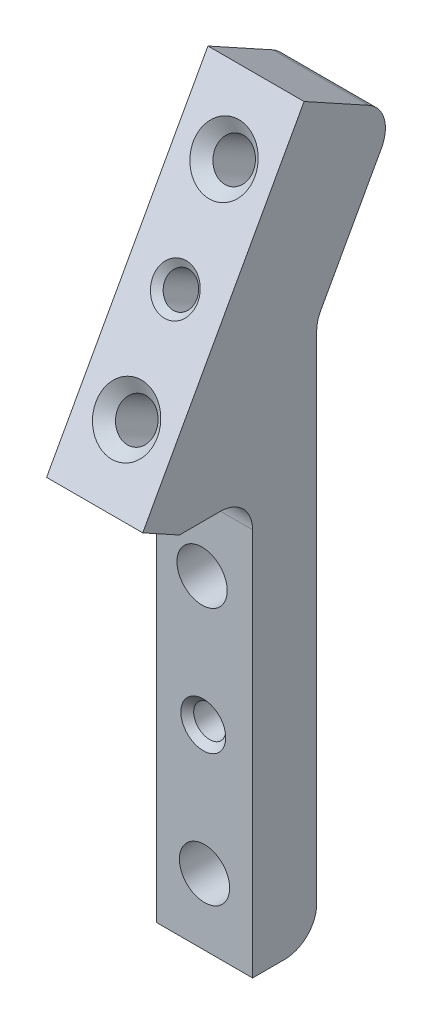
SolidWorks part; units mm, degrees
ref_plane "Front Plane" through (0, 0, 0) normal (0, 0, 1) x (1, 0, 0)
ref_plane "Top Plane" through (0, 0, 0) normal (0, 1, 0) x (1, 0, 0)
ref_plane "Right Plane" through (0, 0, 0) normal (1, 0, 0) x (0, 0, -1)
sketch "Sketch1" plane through (0, 0, 0) normal (1, 0, 0) x (0, 0, -1)
  line L0 (0, 0) -> (13.5105, 24.5248)
  line L1 (0, 0) -> (0, -40)
  line L2 (0, -40) -> (-6.35, -40)
  line L3 (-6.35, -40) -> (-6.35, 1.6334)
  line L4 (-6.35, 1.6334) -> (7.9486, 27.5888)
  line L5 (7.9486, 27.5888) -> (13.5105, 24.5248)
  dimension "D1" = 6.35
  dimension "D2" = 40
  dimension "D3" = 28
  dimension "D4" = 151.15
extrude "Boss-Extrude1" add sketch "Sketch1" along normal blind 9.525
sketch "Sketch2" plane through (0, 3.064, 5.5619) normal (0, 0.4825, 0.8759) x (1, 0, 0)
  line L4 (0, 28) -> (0, -1.6334)
  line L5 (0, -1.6334) -> (9.525, -1.6334)
  line L6 (9.525, -1.6334) -> (9.525, 28)
  line L7 (9.525, 28) -> (0, 28)
  line L8 (0, 28) -> (0, -1.6334)
  line L9 (0, -1.6334) -> (9.525, -1.6334)
  line L10 (9.525, -1.6334) -> (9.525, 28)
  line L11 (9.525, 28) -> (0, 28)
  dimension "D1" = 0
extrude "Boss-Extrude2" add sketch "Sketch2" along normal blind 10.5
sketch "Sketch3" plane through (0, 0, 0) normal (-1, 0, 0) x (0, 0, 1)
  line L0 (15.5468, 6.6998) -> (6.35, 1.6334) construction
  line L1 (1.2482, 32.6552) -> (15.5468, 6.6998) construction
  line L2 (15.5468, 6.6998) -> (6.35, 1.6334)
  line L3 (15.5468, 6.6998) -> (17.2347, 3.6358)
  line L4 (6.35, 1.6334) -> (13.5998, 1.6334)
  line L5 (6.35, 1.6334) -> (6.35, -40) construction
  line L6 (17.2347, 3.6358) -> (13.5998, 1.6334)
  dimension "D1" = 3.4982
extrude "Boss-Extrude3" add sketch "Sketch3" against normal up to surface (9.525 mm away) up to face at (9.525, -2.0695, 2.2835)
sketch "Sketch4" plane through (9.525, 0, 0) normal (1, 0, 0) x (0, 0, -1)
  line L0 (13.5105, 24.5248) -> (-1.2482, 32.6552) construction
  line L1 (0, 0) -> (13.5105, 24.5248) construction
  line L2 (0, -40) -> (0, 0) construction
  line L3 (13.5105, 24.5248) -> (7.9486, 27.5888)
  line L4 (0, 0) -> (13.5105, 24.5248)
  line L5 (0, 0) -> (0, 13.1601)
  line L6 (7.9486, 27.5888) -> (0, 13.1601)
extrude "Cut-Extrude1" cut sketch "Sketch4" against normal up to surface (9.525 mm away) up to face at (0, -1.9897, 3.909)
fillet "Fillet1" radius 3.175 4 edges at (4.7625, -40, 0) (4.7625, 27.5888, -7.9486) (4.7625, 1.6334, 6.35) (4.7625, 13.1601, 0)
hole_wizard "#10-24 Tapped Hole1" positions "Sketch6" profile "Sketch5" tap size "#10-24" standard "Ansi Inch"
sketch "Sketch6" plane through (0, 8.1304, 14.7587) normal (0, 0.4825, 0.8759) x (1, 0, 0)
  line L0 (4.7625, 28) -> (4.7625, 21.4342) construction
  line L1 (9.525, 28) -> (0, 28) construction
  line L2 (4.7625, 21.4342) -> (4.7625, 1.4342) construction
  line L3 (0, 11.4342) -> (4.7625, 11.4342) construction
  line L4 (0, 28) -> (0, -5.1315) construction
  point P0 (4.7625, 21.4342)
  point P1 (4.7625, 1.4342)
  dimension "D1" = 20
sketch "Sketch5" plane through (4.7625, 26.9044, 4.4163) normal (1, 0, 0) x (0, -0.8759, 0.4825)
  line L0 (0, 0) -> (0, 13.9708)
  line L1 (0, 13.9708) -> (1.8986, 12.83)
  line L2 (1.8986, 12.83) -> (1.8986, 1.1494)
  line L3 (1.8986, 1.1494) -> (3.048, 0)
  line L5 (3.048, 0) -> (0, 0)
  line L6 (-1.8986, 1.1493) -> (-3.048, 0) construction
  line L10 (0, 13.9708) -> (-1.8987, 12.83) construction
  line L11 (0, -6.35) -> (0, 107.95) construction
  dimension "Tap Drill Dia." = 3.7973
  dimension "Tap Drill Depth" = 12.83
  dimension "Near C'Sink Dia." = 6.096
  dimension "Near C'Sink Angle" = 90
  dimension "Drill Angle" = 118
cosmetic thread "Hole Thread1" parameters "D1"=9.65, "D2"=4.826
cosmetic thread "Hole Thread2" parameters "D1"=9.65, "D2"=4.826
hole_wizard "1/8 (0.125) Diameter Hole1" positions "Sketch8" profile "Sketch7" hole size "1/8" standard "Ansi Inch"
sketch "Sketch8" plane through (0, 8.1304, 14.7587) normal (0, 0.4825, 0.8759) x (1, 0, 0)
  line L0 (4.7625, 28) -> (4.7625, 11.4342) construction
  line L1 (9.525, 28) -> (0, 28) construction
  line L2 (0, 11.4342) -> (4.7625, 11.4342) construction
  line L3 (0, 28) -> (0, -5.1315) construction
  point P0 (4.7625, 11.4342)
sketch "Sketch7" plane through (4.7625, 18.1455, 9.2414) normal (1, 0, 0) x (0, -0.8759, 0.4825)
  line L0 (0, 0) -> (0, 8.9539)
  line L1 (0, 8.9539) -> (1.5875, 8)
  line L2 (1.5875, 8) -> (1.5875, 0.635)
  line L3 (1.5875, 0.635) -> (2.2225, 0)
  line L5 (2.2225, 0) -> (0, 0)
  line L6 (-1.5875, 0.635) -> (-2.2225, 0) construction
  line L10 (0, 8.9539) -> (-1.5875, 8) construction
  line L11 (0, -6.35) -> (0, 107.95) construction
  dimension "Hole Dia." = 3.175
  dimension "Hole Depth" = 8
  dimension "Near C'Sink Dia." = 4.445
  dimension "Near C'Sink Angle" = 90
  dimension "Drill Angle" = 118
hole_wizard "#10 Clearance Hole1" positions "Sketch10" profile "Sketch11" hole size "#10" standard "Ansi Inch" end condition through all
sketch "Sketch10" plane through (0, 0, 6.35) normal (0, 0, 1) x (1, 0, 0)
  line L0 (4.7625, -40) -> (4.7625, -33.4186) construction
  line L1 (9.525, -40) -> (0, -40) construction
  line L2 (4.7625, -33.4186) -> (4.7625, -8.3547) construction
  line L3 (0, 1.6334) -> (9.525, 1.6334) construction
  point P0 (4.7625, -33.4186)
  point P1 (4.5198, -8.0186)
  dimension "D1" = 9.652
  dimension "D2" = 25.4
sketch "Sketch11" plane through (4.7625, -33.4186, 6.35) normal (1, 0, 0) x (0, -1, 0)
  line L0 (0, 0) -> (0, 13.1607)
  line L1 (0, 13.1607) -> (2.4892, 13.1607)
  line L2 (2.4892, 13.1607) -> (2.4892, 0)
  line L5 (2.4892, 0) -> (0, 0)
  line L11 (0, -6.35) -> (0, 107.95) construction
  dimension "Thru Hole Dia." = 4.9784
  dimension "Thru Hole Depth" = 13.1607
hole_wizard "1/8 (0.125) Diameter Hole2" positions "Sketch13" profile "Sketch12" hole size "1/8" standard "Ansi Inch" end condition through all
sketch "Sketch13" plane through (0, 0, 6.35) normal (0, 0, 1) x (1, 0, 0)
  line L0 (4.7625, -33.4186) -> (4.5198, -8.0186) construction
  point P0 (4.6411, -20.7186)
sketch "Sketch12" plane through (4.6411, -20.7186, 6.35) normal (1, 0, 0) x (0, -1, 0)
  line L0 (0, 0) -> (0, 6.35)
  line L1 (0, 6.35) -> (2.2225, 6.35)
  line L2 (1.5875, 5.715) -> (1.5875, 0.635)
  line L3 (1.5875, 0.635) -> (2.2225, 0)
  line L5 (2.2225, 0) -> (0, 0)
  line L6 (-1.5875, 0.635) -> (-2.2225, 0) construction
  line L7 (2.2225, 6.35) -> (1.5875, 5.715)
  line L8 (-2.2225, 6.35) -> (-1.5875, 5.715) construction
  line L11 (0, -6.35) -> (0, 107.95) construction
  dimension "Thru Hole Dia." = 3.175
  dimension "Thru Hole Depth" = 6.35
  dimension "Near C'Sink Dia." = 4.445
  dimension "Near C'Sink Angle" = 90
  dimension "Far C'Sink Dia." = 4.445
  dimension "Far C'Sink Angle" = 90
